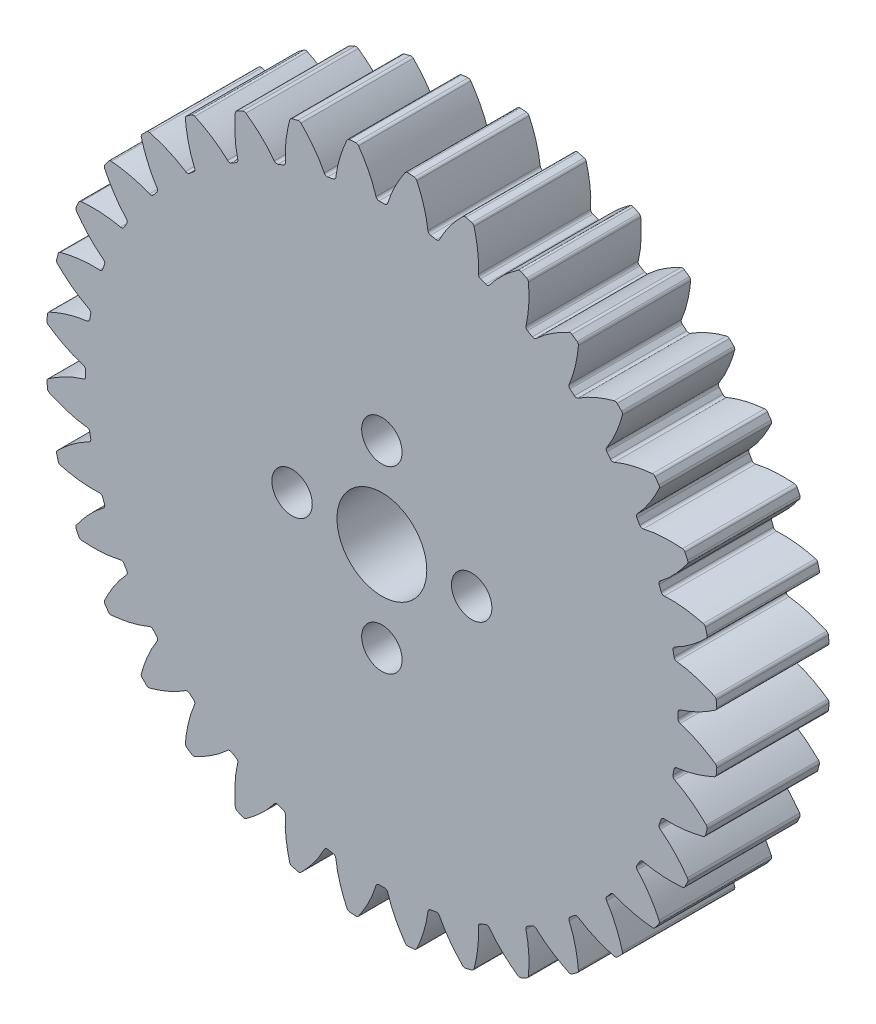
SolidWorks part; units mm, degrees
material "Alloy Steel"
ref_plane "Front" through (0, 0, 0) normal (0, 0, 1) x (1, 0, 0)
ref_plane "Top" through (0, 0, 0) normal (0, 1, 0) x (1, 0, 0)
ref_plane "Right" through (0, 0, 0) normal (1, 0, 0) x (0, 0, -1)
sketch "Sketch1" plane through (0, 0, 0) normal (0, 0, 1) x (1, 0, 0)
  circle A0 centre (0, 0) radius 19
extrude "Boss-Extrude1" add sketch "Sketch1" along normal blind 6.35
sketch "Sketch3" plane through (0, 0, 0) normal (0, 0, 1) x (1, 0, 0)
  line L0 (0, 0) -> (43.7181, 0) construction
  line L2 (0, 0) -> (-0.2288, 16.7484) construction
  line L3 (0, 0) -> (0.2288, 16.7484) construction
  line L4 (0.2288, 16.7484) -> (0.2228, 16.312) construction
  line L5 (0, 0) -> (0, 61.276) construction
  line L6 (-0.2288, 16.7484) -> (-0.2228, 16.312) construction
  circle A0 centre (0, 0) radius 19 construction
  circle A1 centre (0, 0) radius 18 construction
  circle A2 centre (0, 0) radius 16.3135 construction
  arc A3 (0.2288, 16.7484) -> (-0.2288, 16.7484) centre (0, 0) ccw construction
  arc A5 (1.3756, 18.9501) -> (-1.3756, 18.9501) centre (0, 0) ccw
  spline S0 degree 4 poles (-0.2228, 16.312) (-0.2229, 16.3163) (-0.2234, 16.3284) (-0.225, 16.3511) (-0.2285, 16.3882) (-0.2344, 16.4354) (-0.2436, 16.4963) (-0.2564, 16.5679) (-0.2727, 16.6464) (-0.2927, 16.7316) (-0.3146, 16.8163) (-0.3385, 16.9005) (-0.3639, 16.9843) (-0.3967, 17.0854) (-0.4388, 17.2062) (-0.4921, 17.3467) (-0.5572, 17.5052) (-0.6287, 17.6658) (-0.7032, 17.823) (-0.7833, 17.9808) (-0.8641, 18.1327) (-0.9529, 18.2893) (-1.0373, 18.4333) (-1.1372, 18.5932) (-1.2193, 18.7219) (-1.3333, 18.8901) (-1.4024, 18.9889) (-1.4851, 19.1041) (-1.5228, 19.1549) (-1.546, 19.1862) knots 0 0 0 0 0 0.005377 0.015084 0.028532 0.04661 0.064855 0.092111 0.119476 0.146842 0.174209 0.201575 0.228941 0.256307 0.307035 0.361767 0.4165 0.471232 0.525964 0.580697 0.635429 0.690161 0.744894 0.799626 0.854358 0.909091 0.954545 1 1 1 1 1 construction
  spline S1 degree 4 poles (-0.2228, 16.312) (-0.2229, 16.3163) (-0.2234, 16.3284) (-0.225, 16.3511) (-0.2285, 16.3882) (-0.2344, 16.4354) (-0.2436, 16.4963) (-0.2564, 16.5679) (-0.2727, 16.6464) (-0.2927, 16.7316) (-0.3146, 16.8163) (-0.3385, 16.9005) (-0.3639, 16.9843) (-0.3967, 17.0854) (-0.4388, 17.2062) (-0.4921, 17.3467) (-0.5572, 17.5052) (-0.6287, 17.6658) (-0.7032, 17.823) (-0.7833, 17.9808) (-0.8641, 18.1327) (-0.9529, 18.2893) (-1.0373, 18.4333) (-1.1372, 18.5932) (-1.2193, 18.7219) (-1.3086, 18.8536) (-1.3527, 18.9175) (-1.3756, 18.9501) knots 0 0 0 0 0 0.005377 0.015084 0.028532 0.04661 0.064855 0.092111 0.119476 0.146842 0.174209 0.201575 0.228941 0.256307 0.307035 0.361767 0.4165 0.471232 0.525964 0.580697 0.635429 0.690161 0.744894 0.799626 0.854358 0.909091 0.909091 0.909091 0.909091 0.909091
  spline S2 degree 4 poles (0.2228, 16.312) (0.2229, 16.3163) (0.2234, 16.3284) (0.225, 16.3511) (0.2285, 16.3882) (0.2344, 16.4354) (0.2436, 16.4963) (0.2564, 16.5679) (0.2727, 16.6464) (0.2927, 16.7316) (0.3146, 16.8163) (0.3385, 16.9005) (0.3639, 16.9843) (0.3967, 17.0854) (0.4388, 17.2062) (0.4921, 17.3467) (0.5572, 17.5052) (0.6287, 17.6658) (0.7032, 17.823) (0.7833, 17.9808) (0.8641, 18.1327) (0.9529, 18.2893) (1.0373, 18.4333) (1.1372, 18.5932) (1.2193, 18.7219) (1.3333, 18.8901) (1.4024, 18.9889) (1.4851, 19.1041) (1.5228, 19.1549) (1.546, 19.1862) knots 0 0 0 0 0 0.005377 0.015084 0.028532 0.04661 0.064855 0.092111 0.119476 0.146842 0.174209 0.201575 0.228941 0.256307 0.307035 0.361767 0.4165 0.471232 0.525964 0.580697 0.635429 0.690161 0.744894 0.799626 0.854358 0.909091 0.954545 1 1 1 1 1 construction
  spline S3 degree 4 poles (0.2228, 16.312) (0.2229, 16.3163) (0.2234, 16.3284) (0.225, 16.3511) (0.2285, 16.3882) (0.2344, 16.4354) (0.2436, 16.4963) (0.2564, 16.5679) (0.2727, 16.6464) (0.2927, 16.7316) (0.3146, 16.8163) (0.3385, 16.9005) (0.3639, 16.9843) (0.3967, 17.0854) (0.4388, 17.2062) (0.4921, 17.3467) (0.5572, 17.5052) (0.6287, 17.6658) (0.7032, 17.823) (0.7833, 17.9808) (0.8641, 18.1327) (0.9529, 18.2893) (1.0373, 18.4333) (1.1372, 18.5932) (1.2193, 18.7219) (1.3086, 18.8536) (1.3527, 18.9175) (1.3756, 18.9501) knots 0 0 0 0 0 0.005377 0.015084 0.028532 0.04661 0.064855 0.092111 0.119476 0.146842 0.174209 0.201575 0.228941 0.256307 0.307035 0.361767 0.4165 0.471232 0.525964 0.580697 0.635429 0.690161 0.744894 0.799626 0.854358 0.909091 0.909091 0.909091 0.909091 0.909091
  point P0 (0, 16.75)
sketch "DCLTBC" [suppressed] plane through (0, 0, 0) normal (0, 0, 1) x (1, 0, 0)
  line L0 (0, 0) -> (41.04, 0) construction
  line L1 (-0.4038, 9.7416) -> (-0.4129, 9.9608) construction
  line L2 (0.4038, 9.7416) -> (0.4129, 9.9608) construction
  line L3 (-0.4038, 9.7416) -> (-0.4129, 9.9608)
  line L4 (0.4038, 9.7416) -> (0.4129, 9.9608)
  line L5 (0, 0) -> (0, 104.9356) construction
  circle A0 centre (0, 0) radius 12
  circle A1 centre (0, 0) radius 11 construction
  circle A2 centre (0, 0) radius 9.9694 construction
  arc A3 (0.4038, 9.7416) -> (-0.4038, 9.7416) centre (0, 0) ccw construction
  arc A4 (0.4038, 9.7416) -> (-0.4038, 9.7416) centre (0, 0) ccw
  spline S0 degree 4 poles (-998.7217, -47.8614) (-12.2647, 8.3358) (-0.5577, 9.2072) (-0.3666, 9.623) (-0.4193, 10.0193) (-0.4253, 10.0554) (-0.4345, 10.1019) (-0.447, 10.1565) (-0.4626, 10.2161) (-0.4815, 10.2807) (-0.5021, 10.3448) (-0.5242, 10.4085) (-0.5478, 10.4716) (-0.578, 10.5476) (-0.6165, 10.6382) (-0.665, 10.7431) (-0.724, 10.8611) (-0.7884, 10.9801) (-0.8552, 11.0961) (-0.9267, 11.2119) (-0.9987, 11.323) (-1.0775, 11.437) (-1.1522, 11.5414) (-1.2403, 11.6567) (-1.6179, 12.1395) (-3.0339, 13.6814) (15.0543, -7.491) (-654.575, 769.1124) knots -0.603062 -0.603062 -0.603062 -0.603062 -0.603062 0.005377 0.015084 0.028532 0.04661 0.064855 0.092111 0.119476 0.146842 0.174209 0.201575 0.228941 0.256307 0.307035 0.361767 0.4165 0.471232 0.525964 0.580697 0.635429 0.690161 0.744894 0.799626 0.854358 1.832297 1.832297 1.832297 1.832297 1.832297 only from (-0.4129, 9.9608) to (-1.4497, 11.9121) construction
  spline S1 degree 4 poles (998.7217, -47.8614) (12.2647, 8.3358) (0.5577, 9.2072) (0.3666, 9.623) (0.4193, 10.0193) (0.4253, 10.0554) (0.4345, 10.1019) (0.447, 10.1565) (0.4626, 10.2161) (0.4815, 10.2807) (0.5021, 10.3448) (0.5242, 10.4085) (0.5478, 10.4716) (0.578, 10.5476) (0.6165, 10.6382) (0.665, 10.7431) (0.724, 10.8611) (0.7884, 10.9801) (0.8552, 11.0961) (0.9267, 11.2119) (0.9987, 11.323) (1.0775, 11.437) (1.1522, 11.5414) (1.2403, 11.6567) (1.6179, 12.1395) (3.0339, 13.6814) (-15.0543, -7.491) (654.575, 769.1124) knots -0.603062 -0.603062 -0.603062 -0.603062 -0.603062 0.005377 0.015084 0.028532 0.04661 0.064855 0.092111 0.119476 0.146842 0.174209 0.201575 0.228941 0.256307 0.307035 0.361767 0.4165 0.471232 0.525964 0.580697 0.635429 0.690161 0.744894 0.799626 0.854358 1.832297 1.832297 1.832297 1.832297 1.832297 only from (0.4129, 9.9608) to (1.4497, 11.9121) construction
  spline S2 degree 4 poles (-0.4129, 9.9608) (-0.413, 9.9641) (-0.4137, 9.9734) (-0.4155, 9.9909) (-0.4193, 10.0193) (-0.4253, 10.0554) (-0.4345, 10.1019) (-0.447, 10.1565) (-0.4626, 10.2161) (-0.4815, 10.2807) (-0.5021, 10.3448) (-0.5242, 10.4085) (-0.5478, 10.4716) (-0.578, 10.5476) (-0.6165, 10.6382) (-0.665, 10.7431) (-0.724, 10.8611) (-0.7884, 10.9801) (-0.8552, 11.0961) (-0.9267, 11.2119) (-0.9987, 11.323) (-1.0775, 11.437) (-1.1522, 11.5414) (-1.2403, 11.6567) (-1.3127, 11.7493) (-1.3911, 11.8434) (-1.4298, 11.8889) (-1.4497, 11.9121) knots 0 0 0 0 0 0.005377 0.015084 0.028532 0.04661 0.064855 0.092111 0.119476 0.146842 0.174209 0.201575 0.228941 0.256307 0.307035 0.361767 0.4165 0.471232 0.525964 0.580697 0.635429 0.690161 0.744894 0.799626 0.854358 0.909091 0.909091 0.909091 0.909091 0.909091
  spline S3 degree 4 poles (0.4129, 9.9608) (0.413, 9.9641) (0.4137, 9.9734) (0.4155, 9.9909) (0.4193, 10.0193) (0.4253, 10.0554) (0.4345, 10.1019) (0.447, 10.1565) (0.4626, 10.2161) (0.4815, 10.2807) (0.5021, 10.3448) (0.5242, 10.4085) (0.5478, 10.4716) (0.578, 10.5476) (0.6165, 10.6382) (0.665, 10.7431) (0.724, 10.8611) (0.7884, 10.9801) (0.8552, 11.0961) (0.9267, 11.2119) (0.9987, 11.323) (1.0775, 11.437) (1.1522, 11.5414) (1.2403, 11.6567) (1.3127, 11.7493) (1.3911, 11.8434) (1.4298, 11.8889) (1.4497, 11.9121) knots 0 0 0 0 0 0.005377 0.015084 0.028532 0.04661 0.064855 0.092111 0.119476 0.146842 0.174209 0.201575 0.228941 0.256307 0.307035 0.361767 0.4165 0.471232 0.525964 0.580697 0.635429 0.690161 0.744894 0.799626 0.854358 0.909091 0.909091 0.909091 0.909091 0.909091
extrude "Cut-Extrude-DCLTBC" [suppressed] cut sketch "DCLTBC" along normal through all
fillet "Fillet-Tip-DCLTBC" [suppressed] radius 0.1778
fillet "Fillet-Root-DCLTBC" [suppressed] radius 0.3557
pattern_circular "CirPattern-DCLTBC" [suppressed] count 36 over 360
sketch "DCGTBC" plane through (0, 0, 0) normal (0, 0, 1) x (1, 0, 0)
  line L0 (0, 0) -> (41.04, 0) construction
  line L1 (-16.6863, 1.4599) -> (0, 0) construction
  line L2 (0, 0) -> (16.6863, 1.4599) construction
  line L3 (0, 0) -> (-16.5124, 0)
  line L5 (0, 0) -> (0, 104.9356) construction
  circle A0 centre (0, 0) radius 19
  circle A1 centre (0, 0) radius 18 construction
  circle A2 centre (0, 0) radius 16.3135 construction
  arc A3 (0.2288, 16.7484) -> (-0.2288, 16.7484) centre (0, 0) ccw construction
  arc A11 (16.6863, 1.4599) -> (-16.6863, 1.4599) centre (0, 0) ccw
  spline S4 degree 4 poles (999.648, -16.8403) (12.5795, 14.7408) (0.3974, 15.3801) (0.1811, 15.8887) (0.2285, 16.3882) (0.2344, 16.4354) (0.2436, 16.4963) (0.2564, 16.5679) (0.2727, 16.6464) (0.2927, 16.7316) (0.3146, 16.8163) (0.3385, 16.9005) (0.3639, 16.9843) (0.3967, 17.0854) (0.4388, 17.2062) (0.4921, 17.3467) (0.5572, 17.5052) (0.6287, 17.6658) (0.7032, 17.823) (0.7833, 17.9808) (0.8641, 18.1327) (0.9529, 18.2893) (1.0373, 18.4333) (1.1372, 18.5932) (1.5431, 19.229) (3.0107, 21.2099) (-14.0458, -3.3761) (575.092, 837.962) knots -0.580865 -0.580865 -0.580865 -0.580865 -0.580865 0.005377 0.015084 0.028532 0.04661 0.064855 0.092111 0.119476 0.146842 0.174209 0.201575 0.228941 0.256307 0.307035 0.361767 0.4165 0.471232 0.525964 0.580697 0.635429 0.690161 0.744894 0.799626 0.854358 1.771826 1.771826 1.771826 1.771826 1.771826 only from (0.2228, 16.312) to (1.3756, 18.9501) construction
  spline S5 degree 4 poles (-999.648, -16.8403) (-12.5795, 14.7408) (-0.3974, 15.3801) (-0.1811, 15.8887) (-0.2285, 16.3882) (-0.2344, 16.4354) (-0.2436, 16.4963) (-0.2564, 16.5679) (-0.2727, 16.6464) (-0.2927, 16.7316) (-0.3146, 16.8163) (-0.3385, 16.9005) (-0.3639, 16.9843) (-0.3967, 17.0854) (-0.4388, 17.2062) (-0.4921, 17.3467) (-0.5572, 17.5052) (-0.6287, 17.6658) (-0.7032, 17.823) (-0.7833, 17.9808) (-0.8641, 18.1327) (-0.9529, 18.2893) (-1.0373, 18.4333) (-1.1372, 18.5932) (-1.5431, 19.229) (-3.0107, 21.2099) (14.0458, -3.3761) (-575.092, 837.962) knots -0.580865 -0.580865 -0.580865 -0.580865 -0.580865 0.005377 0.015084 0.028532 0.04661 0.064855 0.092111 0.119476 0.146842 0.174209 0.201575 0.228941 0.256307 0.307035 0.361767 0.4165 0.471232 0.525964 0.580697 0.635429 0.690161 0.744894 0.799626 0.854358 1.771826 1.771826 1.771826 1.771826 1.771826 only from (-0.2228, 16.312) to (-1.3756, 18.9501) construction
  spline S6 degree 4 poles (0.2228, 16.312) (0.2229, 16.3163) (0.2234, 16.3284) (0.225, 16.3511) (0.2285, 16.3882) (0.2344, 16.4354) (0.2436, 16.4963) (0.2564, 16.5679) (0.2727, 16.6464) (0.2927, 16.7316) (0.3146, 16.8163) (0.3385, 16.9005) (0.3639, 16.9843) (0.3967, 17.0854) (0.4388, 17.2062) (0.4921, 17.3467) (0.5572, 17.5052) (0.6287, 17.6658) (0.7032, 17.823) (0.7833, 17.9808) (0.8641, 18.1327) (0.9529, 18.2893) (1.0373, 18.4333) (1.1372, 18.5932) (1.2193, 18.7219) (1.3086, 18.8536) (1.3527, 18.9175) (1.3756, 18.9501) knots 0 0 0 0 0 0.005377 0.015084 0.028532 0.04661 0.064855 0.092111 0.119476 0.146842 0.174209 0.201575 0.228941 0.256307 0.307035 0.361767 0.4165 0.471232 0.525964 0.580697 0.635429 0.690161 0.744894 0.799626 0.854358 0.909091 0.909091 0.909091 0.909091 0.909091
  spline S7 degree 4 poles (-0.2228, 16.312) (-0.2229, 16.3163) (-0.2234, 16.3284) (-0.225, 16.3511) (-0.2285, 16.3882) (-0.2344, 16.4354) (-0.2436, 16.4963) (-0.2564, 16.5679) (-0.2727, 16.6464) (-0.2927, 16.7316) (-0.3146, 16.8163) (-0.3385, 16.9005) (-0.3639, 16.9843) (-0.3967, 17.0854) (-0.4388, 17.2062) (-0.4921, 17.3467) (-0.5572, 17.5052) (-0.6287, 17.6658) (-0.7032, 17.823) (-0.7833, 17.9808) (-0.8641, 18.1327) (-0.9529, 18.2893) (-1.0373, 18.4333) (-1.1372, 18.5932) (-1.2193, 18.7219) (-1.3086, 18.8536) (-1.3527, 18.9175) (-1.3756, 18.9501) knots 0 0 0 0 0 0.005377 0.015084 0.028532 0.04661 0.064855 0.092111 0.119476 0.146842 0.174209 0.201575 0.228941 0.256307 0.307035 0.361767 0.4165 0.471232 0.525964 0.580697 0.635429 0.690161 0.744894 0.799626 0.854358 0.909091 0.909091 0.909091 0.909091 0.909091
  dimension "D1" = 5
  dimension "D2" = 5
extrude "Cut-Extrude-DCGTBC" cut sketch "DCGTBC" along normal through all
fillet "Fillet-Tip-DCGTBC" radius 0.1778 4 edges at (1.3756, 18.9501, 3.175) (-1.3756, 18.9501, 3.175) (0.297, 16.7474, 3.175) (-0.297, 16.7474, 3.175)
pattern_circular "CirPattern-DCGTBC" count 36 over 360 about axis through (0, 0, 6.35) along (0, 0, 1) of "Cut-Extrude-DCGTBC", "Fillet-Tip-DCGTBC"
sketch "Sketch4" plane through (0, 0, 6.35) normal (0, 0, 1) x (1, 0, 0)
  circle A0 centre (0, 0) radius 2.54
  dimension "D1" = 5.08
extrude "Cut-Extrude2" cut sketch "Sketch4" against normal through all
sketch "Sketch5" plane through (0, 0, 0) normal (0, 0, 1) x (1, 0, 0)
  circle A0 centre (-5.08, 0) radius 1.143
  circle A1 centre (0, 5.08) radius 1.143
  circle A2 centre (5.08, 0) radius 1.143
  circle A3 centre (0, -5.08) radius 1.143
  point P8 (0, 0)
  point P10 (0, 0)
  point P11 (0, 0)
  point P12 (0, 0)
  point P13 (0, 0)
  dimension "D5" = 2.286
  dimension "D6" = 2.286
  dimension "D7" = 2.286
  dimension "D8" = 2.286
  dimension "D1" = 5.08
  dimension "D2" = 5.08
  dimension "D3" = 5.08
  dimension "D4" = 5.08
extrude "Cut-Extrude7" cut sketch "Sketch5" along normal blind 12.7 contours A2 | A1 | A0 | A3
equation "\"DiametralPitch\"= 25.4'Diametral Pitch"
equation "\"NumTeeth\"= 36'Number of Teeth"
equation "\"PressureAngle\"= 25deg'Pressure Angle"
equation "\"Addendum\"= 1 / \"DiametralPitch\"'Addendum"
equation "\"Dedendum\"= 1.25 / \"DiametralPitch\"'Dedendum"
equation "\"WorkingDepth\"= 2 / \"DiametralPitch\"'Working Depth - here for REF (Not used in building model)"
equation "\"WholeDepth\"= 2.25 / \"DiametralPitch\"'Whole Depth - here for REF (Not used in building model)"
equation "\"Clearance\"= .25 / \"DiametralPitch\"'Clearance"
equation "\"CircularPitch\"= pi / \"DiametralPitch\"'Circular Pitch - here for REF (Not used in building model)"
equation "\"PitchCircle\"= \"NumTeeth\" / \"DiametralPitch\"'Pitch Circle - or - Pitch Diameter"
equation "\"OutsideDiameter\"= ( \"NumTeeth\" + 2 ) / \"DiametralPitch\"'Outside Diameter"
equation "\"Fillet_Root\"= \"Clearance\" * cos ( \"PressureAngle\" ) * tan ( ( 90 + \"PressureAngle\" ) / 2 ) 'Fillet Root"
equation "\"AddendumCircle\"= \"PitchCircle\" + ( 2 * \"Addendum\" )'Addendum Circle - or - Addendum Diameter"
equation "\"DedendumCircle\"= \"PitchCircle\" - ( 2 * \"Dedendum\" )'Dedendum Circle - or - Dedendum Diameter"
equation "\"BaseCircle\"= \"PitchCircle\" * cos ( \"PressureAngle\" )'Base Circle - Base Diameter"
equation "\"PitchAngle\"= 360deg / \"NumTeeth\"'Pitch Angle"
equation "\"Alpha\"= sqr ( \"PitchCircle\" ^ 2 - \"BaseCircle\" ^ 2 ) / \"BaseCircle\" * 180 / PI - \"PressureAngle\"'Alpha - Used for Calculating Beta"
equation "\"Beta\"= ( \"PitchAngle\" / 4 - ( \"Alpha\" - 90 ) )'Beta - Used in definition of the parameters for the parametric equation driven curve"
equation "\"Gamma\"= ( \"PitchAngle\" / 4 - ( \"Alpha\" + 90 ) )'Gamma - Used in definition of the parameters for the parametric equation driven curve"
equation "\"Phi\"= sqr ( ( \"AddendumCircle\" / 2 ) ^ 2 - ( \"BaseCircle\" / 2 ) ^ 2 ) / ( \"BaseCircle\" / 2 )'Phi - Used in definition of the parameters for the parametric equation driven curve"
equation "\"DCGTBC\"= iif ( \"DedendumCircle\" > \"BaseCircle\" , \"unsuppressed\" , \"suppressed\" )'if Dedendum Circle IS GREATER THAN BaseCircle THEN UnsuppressORSuppress FEATURE"
equation "\"DCLTBC\"= iif ( \"DedendumCircle\" - .002 > \"BaseCircle\" , \"suppressed\" , \"unsuppressed\" )'if Dedendum Circle - .002 IS GREATER THAN BaseCircle THEN SuppressORUnsuppress FEATURE"
equation "\"Cut-Extrude-DCGTBC\"= iif ( \"DedendumCircle\" > \"BaseCircle\" , \"unsuppressed\" , \"suppressed\" )'if Dedendum Circle IS GREATER THAN BaseCircle THEN UnsuppressORSuppress FEATURE"
equation "\"Cut-Extrude-DCLTBC\"= iif ( \"DedendumCircle\" - .002 > \"BaseCircle\" , \"suppressed\" , \"unsuppressed\" )'if Dedendum Circle - .002 IS GREATER THAN BaseCircle THEN SuppressORUnsuppress FEATURE"
equation "\"CirPattern-DCGTBC\"= iif ( \"DedendumCircle\" > \"BaseCircle\" , \"unsuppressed\" , \"suppressed\" )'if Dedendum Circle IS GREATER THAN BaseCircle THEN UnsuppressORSuppress FEATURE"
equation "\"CirPattern-DCLTBC\"= iif ( \"DedendumCircle\" - .002 > \"BaseCircle\" , \"suppressed\" , \"unsuppressed\" )'if Dedendum Circle - .002 IS GREATER THAN BaseCircle THEN SuppressORUnsuppress FEATURE"
equation "\"Fillet-Tip-DCGTBC\"= iif ( \"DedendumCircle\" > \"BaseCircle\" , \"unsuppressed\" , \"suppressed\" )'if Dedendum Circle IS GREATER THAN BaseCircle THEN UnsuppressORSuppress FEATURE"
equation "\"Fillet-Tip-DCLTBC\"= iif ( \"DedendumCircle\" - .002 > \"BaseCircle\" , \"suppressed\" , \"unsuppressed\" )'if Dedendum Circle - .002 IS GREATER THAN BaseCircle THEN SuppressORUnsuppress FEATURE"
equation "\"Fillet-Root-DCLTBC\"= iif ( \"DedendumCircle\" - .002 > \"BaseCircle\" , \"suppressed\" , \"unsuppressed\" )'if Dedendum Circle - .002 IS GREATER THAN BaseCircle THEN SuppressORUnsuppress FEATURE"
equation "\"D1@CirPattern-DCGTBC\"= \"NumTeeth\"'Number of Teeth"
equation "\"D1@CirPattern-DCLTBC\"= \"NumTeeth\"'Number of Teeth"
equation "\"D1@Fillet-Tip-DCGTBC\"= \"Fillet_Root\" / 2 'Tip Rad For Large No of Teeth"
equation "\"D1@Fillet-Tip-DCLTBC\"=\"Fillet_Root\" / 2'Tip Rad For Small No of Teeth"
equation "\"D1@Fillet-Root-DCLTBC\"= \"Fillet_Root\"'Fillet Root"
